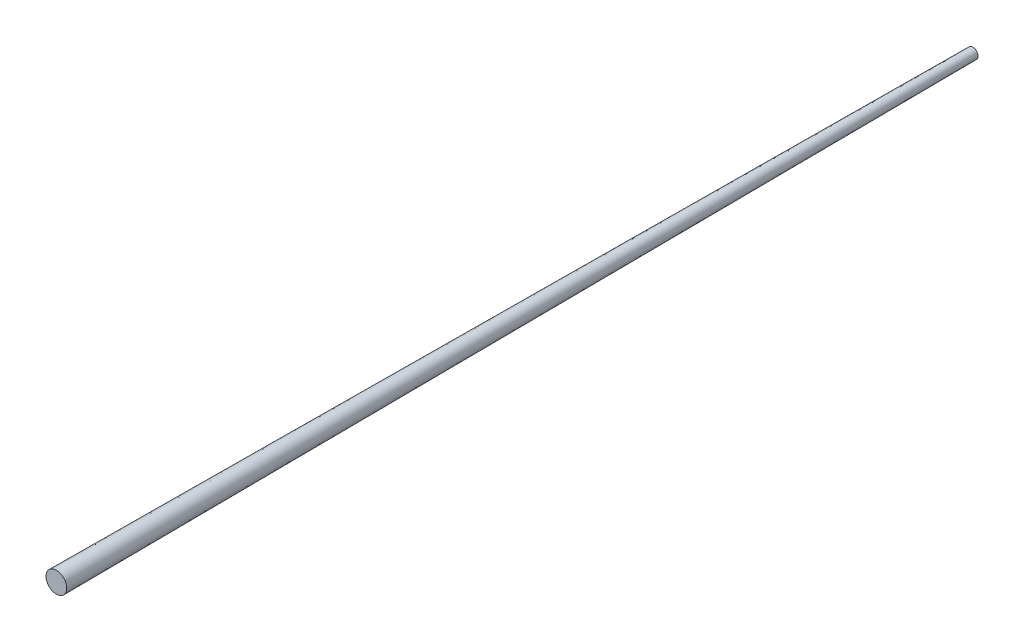
SolidWorks part; units mm, degrees
ref_plane "Front Plane" through (0, 0, 0) normal (0, 0, 1) x (1, 0, 0)
ref_plane "Top Plane" through (0, 0, 0) normal (0, 1, 0) x (1, 0, 0)
ref_plane "Right Plane" through (0, 0, 0) normal (1, 0, 0) x (0, 0, -1)
sketch "Sketch1" plane through (0, 0, 0) normal (0, 1, 0) x (1, 0, 0)
  line L0 (0, 0) -> (4.02, 0)
  line L1 (4.02, 0) -> (2.02, 355.6)
  line L2 (2.02, 355.6) -> (0, 355.6)
  line L3 (0, 355.6) -> (0, 0)
  dimension "D1" = 355.6
  dimension "D2" = 4.02
  dimension "D3" = 2.02
revolve "Revolve1" add sketch "Sketch1" angle 360 about L3
